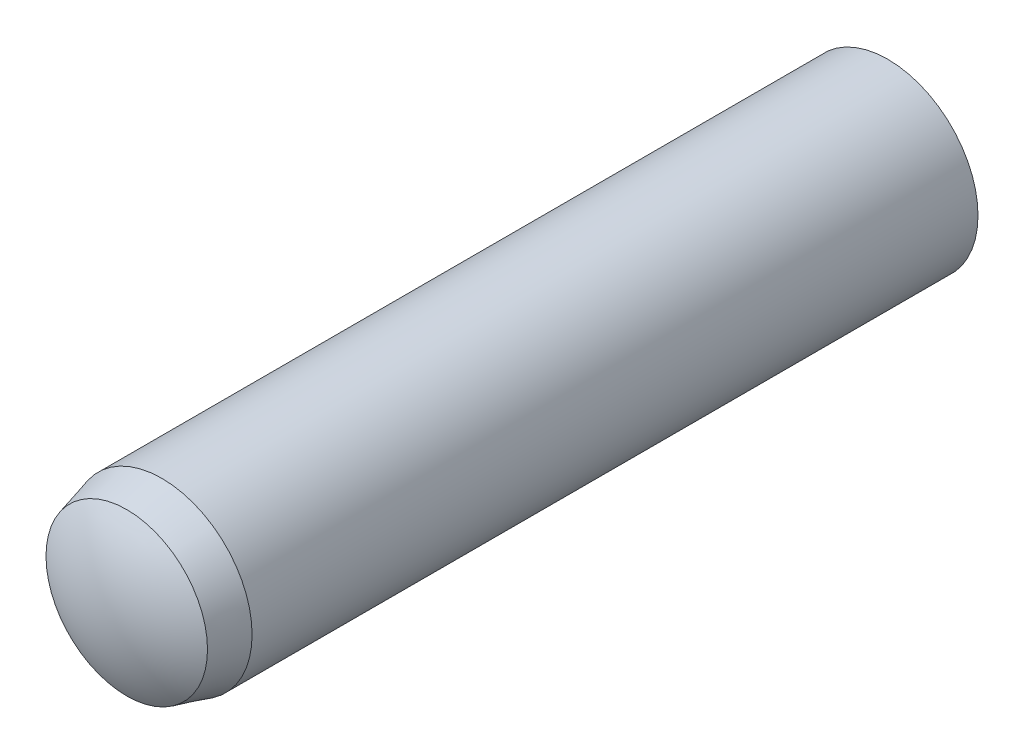
SolidWorks part; units mm, degrees
ref_plane "Front Plane" through (0, 0, 0) normal (0, 0, 1) x (1, 0, 0)
ref_plane "Top Plane" through (0, 0, 0) normal (0, 1, 0) x (1, 0, 0)
ref_plane "Right Plane" through (0, 0, 0) normal (1, 0, 0) x (0, 0, -1)
sketch "Sketch1" plane through (0, 0, 0) normal (0, 0, 1) x (1, 0, 0)
  circle A0 centre (0, 0) radius 4
  point P3 (0, 4)
  dimension "Diameter" = 8
sketch "Sketch2" plane through (0, 0, 0) normal (1, 0, 0) x (0, 0, -1)
  line L0 (-18, 0) -> (18, 0) construction
  line L1 (-18, 0) -> (-18, 4) construction
  line L2 (-18, 4) -> (18, 4)
  line L3 (18, 4) -> (18, 0) construction
  line L4 (-16.96, 3.582) -> (-15.4, 4)
  arc A0 (-18, 0) -> (-16.96, 3.582) centre (-11.3114, 0) cw
  arc A1 (18, 0) -> (16.8, 4) centre (10.7333, 0) ccw
  point P2 (0, 0)
  point P11 (-10, 0)
  point P13 (10, 0)
  dimension "Length" = 36
  dimension "D1" = 15
  dimension "D2" = 1.2
  dimension "D3" = 2.6
  dimension "D4" = 1.56
  dimension "D5" = 8
  dimension "D6" = 8
sketch "Sketch3" plane through (0, 0, 0) normal (1, 0, 0) x (0, 0, -1)
  line L0 (-18, 0) -> (18, 0) construction
  line L1 (-16.96, 3.582) -> (-15.4, 4) construction
  line L2 (-18, 0) -> (18, 0)
  line L3 (-16.96, 3.582) -> (-15.4, 4)
  line L4 (-15.4, 4) -> (16.8, 4)
  arc A0 (18, 0) -> (16.8, 4) centre (10.7333, 0) ccw construction
  arc A1 (-16.96, 3.582) -> (-18, 0) centre (-11.3114, 0) ccw construction
  arc A2 (18, 0) -> (16.8, 4) centre (10.7333, 0) ccw
  arc A3 (-16.96, 3.582) -> (-18, 0) centre (-11.3114, 0) ccw
revolve "Revolve1" add sketch "Sketch3" angle 360 about L2
sketch "Sketch4" plane through (0, 0, 0) normal (0, 1, 0) x (1, 0, 0)
  line L0 (0, 18) -> (0, -18) construction
  line L1 (4, -15.4) -> (-4, -15.4) construction
  line L2 (4, 16.8) -> (-4, 16.8) construction
  line L3 (4, 16.8) -> (4, -15.4) construction
  arc A0 (4, 16.8) -> (-4, 16.8) centre (0, 10.7333) ccw construction
  arc A1 (-3.582, -16.96) -> (3.582, -16.96) centre (0, -11.3114) ccw construction
  dimension "D1" = 36
  dimension "D2" = 2.6
  dimension "D3" = 1.2
  dimension "D4" = 32.2
equation "\"D2@Sketch2\" = \"Diameter@Sketch1\" * .15"
equation "\"D3@Sketch2\" = \"Diameter@Sketch1\" * .325"
equation "\"D4@Sketch2\" = \"D3@Sketch2\" * .6"
equation "\"D5@Sketch2\"=\"Diameter@Sketch1\""
equation "\"D6@Sketch2\"=\"D5@sketch2\""
